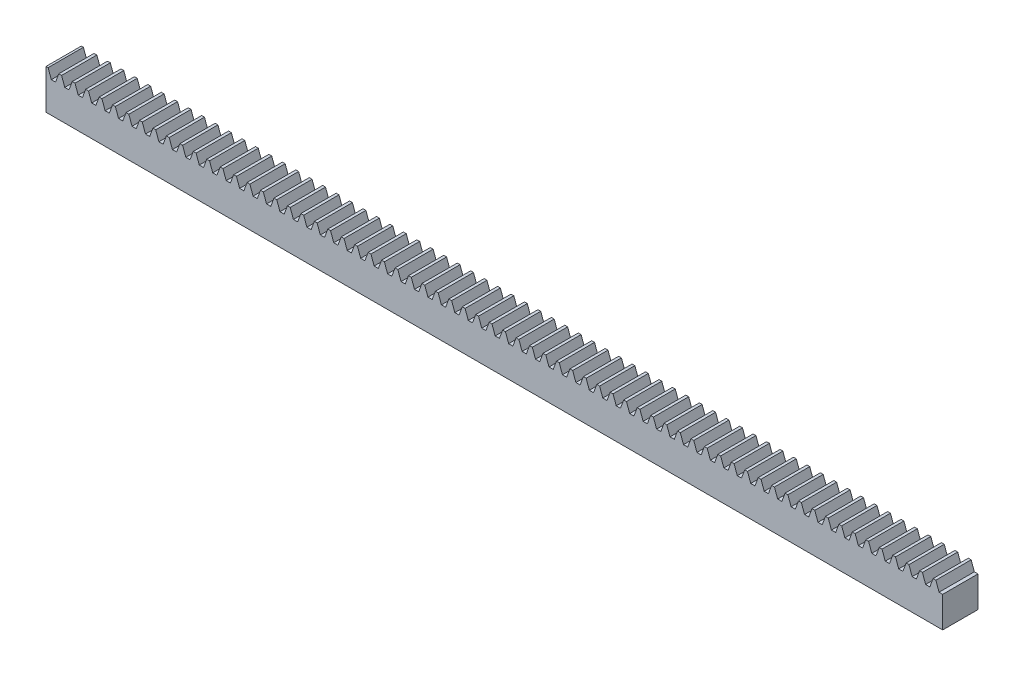
SolidWorks part; units mm, degrees
material "Nylon 101"
ref_plane "Front Plane" through (0, 0, 0) normal (0, 0, 1) x (1, 0, 0)
ref_plane "Top Plane" through (0, 0, 0) normal (0, 1, 0) x (1, 0, 0)
ref_plane "Right Plane" through (0, 0, 0) normal (1, 0, 0) x (0, 0, -1)
sketch "Sketch1" plane through (0, 0, 0) normal (0, 1, 0) x (1, 0, 0)
  line L0 (0, 0) -> (0, 4)
  line L1 (0, 4) -> (101.6, 4)
  line L2 (101.6, 4) -> (101.6, 0)
  line L3 (101.6, 0) -> (0, 0)
  dimension "D1" = 4
  dimension "D2" = 101.6
extrude "Boss-Extrude1" add sketch "Sketch1" along normal blind 4.5
sketch "Sketch2" plane through (0, 0, 0) normal (0, 0, 1) x (1, 0, 0)
  line L0 (0, 4) -> (101.6, 4) construction
  line L1 (0, 4.5) -> (0, 0) construction
  line L2 (101.6, 4.5) -> (101.6, 0) construction
  line L3 (0, 3.5) -> (101.6, 3.5) construction
  line L4 (0, 4.5) -> (101.6, 4.5) construction
  line L5 (0, 4.5) -> (0.239, 4.5) construction
  line L6 (0.239, 4.5) -> (0.603, 3.5)
  line L7 (0.603, 3.5) -> (0.842, 3.5)
  line L8 (1.081, 3.5) -> (1.445, 4.5)
  line L9 (1.445, 4.5) -> (1.684, 4.5) construction
  line L10 (0.842, 3.5) -> (1.081, 3.5)
  line L11 (0.239, 4.5) -> (1.445, 4.5)
  line L12 (1.763, 4.5) -> (2.127, 3.5)
  line L13 (2.127, 3.5) -> (2.366, 3.5)
  line L14 (2.605, 3.5) -> (2.969, 4.5)
  line L15 (2.366, 3.5) -> (2.605, 3.5)
  line L16 (1.763, 4.5) -> (2.969, 4.5)
  line L17 (1.524, 4.5) -> (1.763, 4.5) construction
  line L18 (2.969, 4.5) -> (3.208, 4.5) construction
  line L19 (3.287, 4.5) -> (3.651, 3.5)
  line L20 (3.651, 3.5) -> (3.89, 3.5)
  line L21 (4.129, 3.5) -> (4.493, 4.5)
  line L22 (3.89, 3.5) -> (4.129, 3.5)
  line L23 (3.287, 4.5) -> (4.493, 4.5)
  line L24 (3.048, 4.5) -> (3.287, 4.5) construction
  line L25 (4.493, 4.5) -> (4.732, 4.5) construction
  line L26 (4.811, 4.5) -> (5.175, 3.5)
  line L27 (5.175, 3.5) -> (5.414, 3.5)
  line L28 (5.653, 3.5) -> (6.017, 4.5)
  line L29 (5.414, 3.5) -> (5.653, 3.5)
  line L30 (4.811, 4.5) -> (6.017, 4.5)
  line L31 (4.572, 4.5) -> (4.811, 4.5) construction
  line L32 (6.017, 4.5) -> (6.256, 4.5) construction
  line L33 (6.335, 4.5) -> (6.699, 3.5)
  line L34 (6.699, 3.5) -> (6.938, 3.5)
  line L35 (7.177, 3.5) -> (7.541, 4.5)
  line L36 (6.938, 3.5) -> (7.177, 3.5)
  line L37 (6.335, 4.5) -> (7.541, 4.5)
  line L38 (6.096, 4.5) -> (6.335, 4.5) construction
  line L39 (7.541, 4.5) -> (7.78, 4.5) construction
  line L40 (7.859, 4.5) -> (8.223, 3.5)
  line L41 (8.223, 3.5) -> (8.462, 3.5)
  line L42 (8.701, 3.5) -> (9.065, 4.5)
  line L43 (8.462, 3.5) -> (8.701, 3.5)
  line L44 (7.859, 4.5) -> (9.065, 4.5)
  line L45 (7.62, 4.5) -> (7.859, 4.5) construction
  line L46 (9.065, 4.5) -> (9.304, 4.5) construction
  line L47 (9.383, 4.5) -> (9.747, 3.5)
  line L48 (9.747, 3.5) -> (9.986, 3.5)
  line L49 (10.225, 3.5) -> (10.589, 4.5)
  line L50 (9.986, 3.5) -> (10.225, 3.5)
  line L51 (9.383, 4.5) -> (10.589, 4.5)
  line L52 (9.144, 4.5) -> (9.383, 4.5) construction
  line L53 (10.589, 4.5) -> (10.828, 4.5) construction
  line L54 (10.907, 4.5) -> (11.271, 3.5)
  line L55 (11.271, 3.5) -> (11.51, 3.5)
  line L56 (11.749, 3.5) -> (12.113, 4.5)
  line L57 (11.51, 3.5) -> (11.749, 3.5)
  line L58 (10.907, 4.5) -> (12.113, 4.5)
  line L59 (10.668, 4.5) -> (10.907, 4.5) construction
  line L60 (12.113, 4.5) -> (12.352, 4.5) construction
  line L61 (12.431, 4.5) -> (12.795, 3.5)
  line L62 (12.795, 3.5) -> (13.034, 3.5)
  line L63 (13.273, 3.5) -> (13.637, 4.5)
  line L64 (13.034, 3.5) -> (13.273, 3.5)
  line L65 (12.431, 4.5) -> (13.637, 4.5)
  line L66 (12.192, 4.5) -> (12.431, 4.5) construction
  line L67 (13.637, 4.5) -> (13.876, 4.5) construction
  line L68 (13.955, 4.5) -> (14.319, 3.5)
  line L69 (14.319, 3.5) -> (14.558, 3.5)
  line L70 (14.797, 3.5) -> (15.161, 4.5)
  line L71 (14.558, 3.5) -> (14.797, 3.5)
  line L72 (13.955, 4.5) -> (15.161, 4.5)
  line L73 (13.716, 4.5) -> (13.955, 4.5) construction
  line L74 (15.161, 4.5) -> (15.4, 4.5) construction
  line L75 (15.479, 4.5) -> (15.843, 3.5)
  line L76 (15.843, 3.5) -> (16.082, 3.5)
  line L77 (16.321, 3.5) -> (16.685, 4.5)
  line L78 (16.082, 3.5) -> (16.321, 3.5)
  line L79 (15.479, 4.5) -> (16.685, 4.5)
  line L80 (15.24, 4.5) -> (15.479, 4.5) construction
  line L81 (16.685, 4.5) -> (16.924, 4.5) construction
  line L82 (17.003, 4.5) -> (17.367, 3.5)
  line L83 (17.367, 3.5) -> (17.606, 3.5)
  line L84 (17.845, 3.5) -> (18.209, 4.5)
  line L85 (17.606, 3.5) -> (17.845, 3.5)
  line L86 (17.003, 4.5) -> (18.209, 4.5)
  line L87 (16.764, 4.5) -> (17.003, 4.5) construction
  line L88 (18.209, 4.5) -> (18.448, 4.5) construction
  line L89 (18.527, 4.5) -> (18.891, 3.5)
  line L90 (18.891, 3.5) -> (19.13, 3.5)
  line L91 (19.369, 3.5) -> (19.733, 4.5)
  line L92 (19.13, 3.5) -> (19.369, 3.5)
  line L93 (18.527, 4.5) -> (19.733, 4.5)
  line L94 (18.288, 4.5) -> (18.527, 4.5) construction
  line L95 (19.733, 4.5) -> (19.972, 4.5) construction
  line L96 (20.051, 4.5) -> (20.415, 3.5)
  line L97 (20.415, 3.5) -> (20.654, 3.5)
  line L98 (20.893, 3.5) -> (21.257, 4.5)
  line L99 (20.654, 3.5) -> (20.893, 3.5)
  line L100 (20.051, 4.5) -> (21.257, 4.5)
  line L101 (19.812, 4.5) -> (20.051, 4.5) construction
  line L102 (21.257, 4.5) -> (21.496, 4.5) construction
  line L103 (21.575, 4.5) -> (21.939, 3.5)
  line L104 (21.939, 3.5) -> (22.178, 3.5)
  line L105 (22.417, 3.5) -> (22.781, 4.5)
  line L106 (22.178, 3.5) -> (22.417, 3.5)
  line L107 (21.575, 4.5) -> (22.781, 4.5)
  line L108 (21.336, 4.5) -> (21.575, 4.5) construction
  line L109 (22.781, 4.5) -> (23.02, 4.5) construction
  line L110 (23.099, 4.5) -> (23.463, 3.5)
  line L111 (23.463, 3.5) -> (23.702, 3.5)
  line L112 (23.941, 3.5) -> (24.305, 4.5)
  line L113 (23.702, 3.5) -> (23.941, 3.5)
  line L114 (23.099, 4.5) -> (24.305, 4.5)
  line L115 (22.86, 4.5) -> (23.099, 4.5) construction
  line L116 (24.305, 4.5) -> (24.544, 4.5) construction
  line L117 (24.623, 4.5) -> (24.987, 3.5)
  line L118 (24.987, 3.5) -> (25.226, 3.5)
  line L119 (25.465, 3.5) -> (25.829, 4.5)
  line L120 (25.226, 3.5) -> (25.465, 3.5)
  line L121 (24.623, 4.5) -> (25.829, 4.5)
  line L122 (24.384, 4.5) -> (24.623, 4.5) construction
  line L123 (25.829, 4.5) -> (26.068, 4.5) construction
  line L124 (26.147, 4.5) -> (26.511, 3.5)
  line L125 (26.511, 3.5) -> (26.75, 3.5)
  line L126 (26.989, 3.5) -> (27.353, 4.5)
  line L127 (26.75, 3.5) -> (26.989, 3.5)
  line L128 (26.147, 4.5) -> (27.353, 4.5)
  line L129 (25.908, 4.5) -> (26.147, 4.5) construction
  line L130 (27.353, 4.5) -> (27.592, 4.5) construction
  line L131 (27.671, 4.5) -> (28.035, 3.5)
  line L132 (28.035, 3.5) -> (28.274, 3.5)
  line L133 (28.513, 3.5) -> (28.877, 4.5)
  line L134 (28.274, 3.5) -> (28.513, 3.5)
  line L135 (27.671, 4.5) -> (28.877, 4.5)
  line L136 (27.432, 4.5) -> (27.671, 4.5) construction
  line L137 (28.877, 4.5) -> (29.116, 4.5) construction
  line L138 (29.195, 4.5) -> (29.559, 3.5)
  line L139 (29.559, 3.5) -> (29.798, 3.5)
  line L140 (30.037, 3.5) -> (30.401, 4.5)
  line L141 (29.798, 3.5) -> (30.037, 3.5)
  line L142 (29.195, 4.5) -> (30.401, 4.5)
  line L143 (28.956, 4.5) -> (29.195, 4.5) construction
  line L144 (30.401, 4.5) -> (30.64, 4.5) construction
  line L145 (30.719, 4.5) -> (31.083, 3.5)
  line L146 (31.083, 3.5) -> (31.322, 3.5)
  line L147 (31.561, 3.5) -> (31.925, 4.5)
  line L148 (31.322, 3.5) -> (31.561, 3.5)
  line L149 (30.719, 4.5) -> (31.925, 4.5)
  line L150 (30.48, 4.5) -> (30.719, 4.5) construction
  line L151 (31.925, 4.5) -> (32.164, 4.5) construction
  line L152 (32.243, 4.5) -> (32.607, 3.5)
  line L153 (32.607, 3.5) -> (32.846, 3.5)
  line L154 (33.085, 3.5) -> (33.449, 4.5)
  line L155 (32.846, 3.5) -> (33.085, 3.5)
  line L156 (32.243, 4.5) -> (33.449, 4.5)
  line L157 (32.004, 4.5) -> (32.243, 4.5) construction
  line L158 (33.449, 4.5) -> (33.688, 4.5) construction
  line L159 (33.767, 4.5) -> (34.131, 3.5)
  line L160 (34.131, 3.5) -> (34.37, 3.5)
  line L161 (34.609, 3.5) -> (34.973, 4.5)
  line L162 (34.37, 3.5) -> (34.609, 3.5)
  line L163 (33.767, 4.5) -> (34.973, 4.5)
  line L164 (33.528, 4.5) -> (33.767, 4.5) construction
  line L165 (34.973, 4.5) -> (35.212, 4.5) construction
  line L166 (35.291, 4.5) -> (35.655, 3.5)
  line L167 (35.655, 3.5) -> (35.894, 3.5)
  line L168 (36.133, 3.5) -> (36.497, 4.5)
  line L169 (35.894, 3.5) -> (36.133, 3.5)
  line L170 (35.291, 4.5) -> (36.497, 4.5)
  line L171 (35.052, 4.5) -> (35.291, 4.5) construction
  line L172 (36.497, 4.5) -> (36.736, 4.5) construction
  line L173 (36.815, 4.5) -> (37.179, 3.5)
  line L174 (37.179, 3.5) -> (37.418, 3.5)
  line L175 (37.657, 3.5) -> (38.021, 4.5)
  line L176 (37.418, 3.5) -> (37.657, 3.5)
  line L177 (36.815, 4.5) -> (38.021, 4.5)
  line L178 (36.576, 4.5) -> (36.815, 4.5) construction
  line L179 (38.021, 4.5) -> (38.26, 4.5) construction
  line L180 (38.339, 4.5) -> (38.703, 3.5)
  line L181 (38.703, 3.5) -> (38.942, 3.5)
  line L182 (39.181, 3.5) -> (39.545, 4.5)
  line L183 (38.942, 3.5) -> (39.181, 3.5)
  line L184 (38.339, 4.5) -> (39.545, 4.5)
  line L185 (38.1, 4.5) -> (38.339, 4.5) construction
  line L186 (39.545, 4.5) -> (39.784, 4.5) construction
  line L187 (39.863, 4.5) -> (40.227, 3.5)
  line L188 (40.227, 3.5) -> (40.466, 3.5)
  line L189 (40.705, 3.5) -> (41.069, 4.5)
  line L190 (40.466, 3.5) -> (40.705, 3.5)
  line L191 (39.863, 4.5) -> (41.069, 4.5)
  line L192 (39.624, 4.5) -> (39.863, 4.5) construction
  line L193 (41.069, 4.5) -> (41.308, 4.5) construction
  line L194 (41.387, 4.5) -> (41.751, 3.5)
  line L195 (41.751, 3.5) -> (41.99, 3.5)
  line L196 (42.229, 3.5) -> (42.593, 4.5)
  line L197 (41.99, 3.5) -> (42.229, 3.5)
  line L198 (41.387, 4.5) -> (42.593, 4.5)
  line L199 (41.148, 4.5) -> (41.387, 4.5) construction
  line L200 (42.593, 4.5) -> (42.832, 4.5) construction
  line L201 (42.911, 4.5) -> (43.275, 3.5)
  line L202 (43.275, 3.5) -> (43.514, 3.5)
  line L203 (43.753, 3.5) -> (44.117, 4.5)
  line L204 (43.514, 3.5) -> (43.753, 3.5)
  line L205 (42.911, 4.5) -> (44.117, 4.5)
  line L206 (42.672, 4.5) -> (42.911, 4.5) construction
  line L207 (44.117, 4.5) -> (44.356, 4.5) construction
  line L208 (44.435, 4.5) -> (44.799, 3.5)
  line L209 (44.799, 3.5) -> (45.038, 3.5)
  line L210 (45.277, 3.5) -> (45.641, 4.5)
  line L211 (45.038, 3.5) -> (45.277, 3.5)
  line L212 (44.435, 4.5) -> (45.641, 4.5)
  line L213 (44.196, 4.5) -> (44.435, 4.5) construction
  line L214 (45.641, 4.5) -> (45.88, 4.5) construction
  line L215 (45.959, 4.5) -> (46.323, 3.5)
  line L216 (46.323, 3.5) -> (46.562, 3.5)
  line L217 (46.801, 3.5) -> (47.165, 4.5)
  line L218 (46.562, 3.5) -> (46.801, 3.5)
  line L219 (45.959, 4.5) -> (47.165, 4.5)
  line L220 (45.72, 4.5) -> (45.959, 4.5) construction
  line L221 (47.165, 4.5) -> (47.404, 4.5) construction
  line L222 (47.483, 4.5) -> (47.847, 3.5)
  line L223 (47.847, 3.5) -> (48.086, 3.5)
  line L224 (48.325, 3.5) -> (48.689, 4.5)
  line L225 (48.086, 3.5) -> (48.325, 3.5)
  line L226 (47.483, 4.5) -> (48.689, 4.5)
  line L227 (47.244, 4.5) -> (47.483, 4.5) construction
  line L228 (48.689, 4.5) -> (48.928, 4.5) construction
  line L229 (49.007, 4.5) -> (49.371, 3.5)
  line L230 (49.371, 3.5) -> (49.61, 3.5)
  line L231 (49.849, 3.5) -> (50.213, 4.5)
  line L232 (49.61, 3.5) -> (49.849, 3.5)
  line L233 (49.007, 4.5) -> (50.213, 4.5)
  line L234 (48.768, 4.5) -> (49.007, 4.5) construction
  line L235 (50.213, 4.5) -> (50.452, 4.5) construction
  line L236 (50.531, 4.5) -> (50.895, 3.5)
  line L237 (50.895, 3.5) -> (51.134, 3.5)
  line L238 (51.373, 3.5) -> (51.737, 4.5)
  line L239 (51.134, 3.5) -> (51.373, 3.5)
  line L240 (50.531, 4.5) -> (51.737, 4.5)
  line L241 (50.292, 4.5) -> (50.531, 4.5) construction
  line L242 (51.737, 4.5) -> (51.976, 4.5) construction
  line L243 (52.055, 4.5) -> (52.419, 3.5)
  line L244 (52.419, 3.5) -> (52.658, 3.5)
  line L245 (52.897, 3.5) -> (53.261, 4.5)
  line L246 (52.658, 3.5) -> (52.897, 3.5)
  line L247 (52.055, 4.5) -> (53.261, 4.5)
  line L248 (51.816, 4.5) -> (52.055, 4.5) construction
  line L249 (53.261, 4.5) -> (53.5, 4.5) construction
  line L250 (53.579, 4.5) -> (53.943, 3.5)
  line L251 (53.943, 3.5) -> (54.182, 3.5)
  line L252 (54.421, 3.5) -> (54.785, 4.5)
  line L253 (54.182, 3.5) -> (54.421, 3.5)
  line L254 (53.579, 4.5) -> (54.785, 4.5)
  line L255 (53.34, 4.5) -> (53.579, 4.5) construction
  line L256 (54.785, 4.5) -> (55.024, 4.5) construction
  line L257 (55.103, 4.5) -> (55.467, 3.5)
  line L258 (55.467, 3.5) -> (55.706, 3.5)
  line L259 (55.945, 3.5) -> (56.309, 4.5)
  line L260 (55.706, 3.5) -> (55.945, 3.5)
  line L261 (55.103, 4.5) -> (56.309, 4.5)
  line L262 (54.864, 4.5) -> (55.103, 4.5) construction
  line L263 (56.309, 4.5) -> (56.548, 4.5) construction
  line L264 (56.627, 4.5) -> (56.991, 3.5)
  line L265 (56.991, 3.5) -> (57.23, 3.5)
  line L266 (57.469, 3.5) -> (57.833, 4.5)
  line L267 (57.23, 3.5) -> (57.469, 3.5)
  line L268 (56.627, 4.5) -> (57.833, 4.5)
  line L269 (56.388, 4.5) -> (56.627, 4.5) construction
  line L270 (57.833, 4.5) -> (58.072, 4.5) construction
  line L271 (58.151, 4.5) -> (58.515, 3.5)
  line L272 (58.515, 3.5) -> (58.754, 3.5)
  line L273 (58.993, 3.5) -> (59.357, 4.5)
  line L274 (58.754, 3.5) -> (58.993, 3.5)
  line L275 (58.151, 4.5) -> (59.357, 4.5)
  line L276 (57.912, 4.5) -> (58.151, 4.5) construction
  line L277 (59.357, 4.5) -> (59.596, 4.5) construction
  line L278 (59.675, 4.5) -> (60.039, 3.5)
  line L279 (60.039, 3.5) -> (60.278, 3.5)
  line L280 (60.517, 3.5) -> (60.881, 4.5)
  line L281 (60.278, 3.5) -> (60.517, 3.5)
  line L282 (59.675, 4.5) -> (60.881, 4.5)
  line L283 (59.436, 4.5) -> (59.675, 4.5) construction
  line L284 (60.881, 4.5) -> (61.12, 4.5) construction
  line L285 (61.199, 4.5) -> (61.563, 3.5)
  line L286 (61.563, 3.5) -> (61.802, 3.5)
  line L287 (62.041, 3.5) -> (62.405, 4.5)
  line L288 (61.802, 3.5) -> (62.041, 3.5)
  line L289 (61.199, 4.5) -> (62.405, 4.5)
  line L290 (60.96, 4.5) -> (61.199, 4.5) construction
  line L291 (62.405, 4.5) -> (62.644, 4.5) construction
  line L292 (62.723, 4.5) -> (63.087, 3.5)
  line L293 (63.087, 3.5) -> (63.326, 3.5)
  line L294 (63.565, 3.5) -> (63.929, 4.5)
  line L295 (63.326, 3.5) -> (63.565, 3.5)
  line L296 (62.723, 4.5) -> (63.929, 4.5)
  line L297 (62.484, 4.5) -> (62.723, 4.5) construction
  line L298 (63.929, 4.5) -> (64.168, 4.5) construction
  line L299 (64.247, 4.5) -> (64.611, 3.5)
  line L300 (64.611, 3.5) -> (64.85, 3.5)
  line L301 (65.089, 3.5) -> (65.453, 4.5)
  line L302 (64.85, 3.5) -> (65.089, 3.5)
  line L303 (64.247, 4.5) -> (65.453, 4.5)
  line L304 (64.008, 4.5) -> (64.247, 4.5) construction
  line L305 (65.453, 4.5) -> (65.692, 4.5) construction
  line L306 (65.771, 4.5) -> (66.135, 3.5)
  line L307 (66.135, 3.5) -> (66.374, 3.5)
  line L308 (66.613, 3.5) -> (66.977, 4.5)
  line L309 (66.374, 3.5) -> (66.613, 3.5)
  line L310 (65.771, 4.5) -> (66.977, 4.5)
  line L311 (65.532, 4.5) -> (65.771, 4.5) construction
  line L312 (66.977, 4.5) -> (67.216, 4.5) construction
  line L313 (67.295, 4.5) -> (67.659, 3.5)
  line L314 (67.659, 3.5) -> (67.898, 3.5)
  line L315 (68.137, 3.5) -> (68.501, 4.5)
  line L316 (67.898, 3.5) -> (68.137, 3.5)
  line L317 (67.295, 4.5) -> (68.501, 4.5)
  line L318 (67.056, 4.5) -> (67.295, 4.5) construction
  line L319 (68.501, 4.5) -> (68.74, 4.5) construction
  line L320 (68.819, 4.5) -> (69.183, 3.5)
  line L321 (69.183, 3.5) -> (69.422, 3.5)
  line L322 (69.661, 3.5) -> (70.025, 4.5)
  line L323 (69.422, 3.5) -> (69.661, 3.5)
  line L324 (68.819, 4.5) -> (70.025, 4.5)
  line L325 (68.58, 4.5) -> (68.819, 4.5) construction
  line L326 (70.025, 4.5) -> (70.264, 4.5) construction
  line L327 (70.343, 4.5) -> (70.707, 3.5)
  line L328 (70.707, 3.5) -> (70.946, 3.5)
  line L329 (71.185, 3.5) -> (71.549, 4.5)
  line L330 (70.946, 3.5) -> (71.185, 3.5)
  line L331 (70.343, 4.5) -> (71.549, 4.5)
  line L332 (70.104, 4.5) -> (70.343, 4.5) construction
  line L333 (71.549, 4.5) -> (71.788, 4.5) construction
  line L334 (71.867, 4.5) -> (72.231, 3.5)
  line L335 (72.231, 3.5) -> (72.47, 3.5)
  line L336 (72.709, 3.5) -> (73.073, 4.5)
  line L337 (72.47, 3.5) -> (72.709, 3.5)
  line L338 (71.867, 4.5) -> (73.073, 4.5)
  line L339 (71.628, 4.5) -> (71.867, 4.5) construction
  line L340 (73.073, 4.5) -> (73.312, 4.5) construction
  line L341 (73.391, 4.5) -> (73.755, 3.5)
  line L342 (73.755, 3.5) -> (73.994, 3.5)
  line L343 (74.233, 3.5) -> (74.597, 4.5)
  line L344 (73.994, 3.5) -> (74.233, 3.5)
  line L345 (73.391, 4.5) -> (74.597, 4.5)
  line L346 (73.152, 4.5) -> (73.391, 4.5) construction
  line L347 (74.597, 4.5) -> (74.836, 4.5) construction
  line L348 (74.915, 4.5) -> (75.279, 3.5)
  line L349 (75.279, 3.5) -> (75.518, 3.5)
  line L350 (75.757, 3.5) -> (76.121, 4.5)
  line L351 (75.518, 3.5) -> (75.757, 3.5)
  line L352 (74.915, 4.5) -> (76.121, 4.5)
  line L353 (74.676, 4.5) -> (74.915, 4.5) construction
  line L354 (76.121, 4.5) -> (76.36, 4.5) construction
  line L355 (76.439, 4.5) -> (76.803, 3.5)
  line L356 (76.803, 3.5) -> (77.042, 3.5)
  line L357 (77.281, 3.5) -> (77.645, 4.5)
  line L358 (77.042, 3.5) -> (77.281, 3.5)
  line L359 (76.439, 4.5) -> (77.645, 4.5)
  line L360 (76.2, 4.5) -> (76.439, 4.5) construction
  line L361 (77.645, 4.5) -> (77.884, 4.5) construction
  line L362 (77.963, 4.5) -> (78.327, 3.5)
  line L363 (78.327, 3.5) -> (78.566, 3.5)
  line L364 (78.805, 3.5) -> (79.169, 4.5)
  line L365 (78.566, 3.5) -> (78.805, 3.5)
  line L366 (77.963, 4.5) -> (79.169, 4.5)
  line L367 (77.724, 4.5) -> (77.963, 4.5) construction
  line L368 (79.169, 4.5) -> (79.408, 4.5) construction
  line L369 (79.487, 4.5) -> (79.851, 3.5)
  line L370 (79.851, 3.5) -> (80.09, 3.5)
  line L371 (80.329, 3.5) -> (80.693, 4.5)
  line L372 (80.09, 3.5) -> (80.329, 3.5)
  line L373 (79.487, 4.5) -> (80.693, 4.5)
  line L374 (79.248, 4.5) -> (79.487, 4.5) construction
  line L375 (80.693, 4.5) -> (80.932, 4.5) construction
  line L376 (81.011, 4.5) -> (81.375, 3.5)
  line L377 (81.375, 3.5) -> (81.614, 3.5)
  line L378 (81.853, 3.5) -> (82.217, 4.5)
  line L379 (81.614, 3.5) -> (81.853, 3.5)
  line L380 (81.011, 4.5) -> (82.217, 4.5)
  line L381 (80.772, 4.5) -> (81.011, 4.5) construction
  line L382 (82.217, 4.5) -> (82.456, 4.5) construction
  line L383 (82.535, 4.5) -> (82.899, 3.5)
  line L384 (82.899, 3.5) -> (83.138, 3.5)
  line L385 (83.377, 3.5) -> (83.741, 4.5)
  line L386 (83.138, 3.5) -> (83.377, 3.5)
  line L387 (82.535, 4.5) -> (83.741, 4.5)
  line L388 (82.296, 4.5) -> (82.535, 4.5) construction
  line L389 (83.741, 4.5) -> (83.98, 4.5) construction
  line L390 (84.059, 4.5) -> (84.423, 3.5)
  line L391 (84.423, 3.5) -> (84.662, 3.5)
  line L392 (84.901, 3.5) -> (85.265, 4.5)
  line L393 (84.662, 3.5) -> (84.901, 3.5)
  line L394 (84.059, 4.5) -> (85.265, 4.5)
  line L395 (83.82, 4.5) -> (84.059, 4.5) construction
  line L396 (85.265, 4.5) -> (85.504, 4.5) construction
  line L397 (85.583, 4.5) -> (85.947, 3.5)
  line L398 (85.947, 3.5) -> (86.186, 3.5)
  line L399 (86.425, 3.5) -> (86.789, 4.5)
  line L400 (86.186, 3.5) -> (86.425, 3.5)
  line L401 (85.583, 4.5) -> (86.789, 4.5)
  line L402 (85.344, 4.5) -> (85.583, 4.5) construction
  line L403 (86.789, 4.5) -> (87.028, 4.5) construction
  line L404 (87.107, 4.5) -> (87.471, 3.5)
  line L405 (87.471, 3.5) -> (87.71, 3.5)
  line L406 (87.949, 3.5) -> (88.313, 4.5)
  line L407 (87.71, 3.5) -> (87.949, 3.5)
  line L408 (87.107, 4.5) -> (88.313, 4.5)
  line L409 (86.868, 4.5) -> (87.107, 4.5) construction
  line L410 (88.313, 4.5) -> (88.552, 4.5) construction
  line L411 (88.631, 4.5) -> (88.995, 3.5)
  line L412 (88.995, 3.5) -> (89.234, 3.5)
  line L413 (89.473, 3.5) -> (89.837, 4.5)
  line L414 (89.234, 3.5) -> (89.473, 3.5)
  line L415 (88.631, 4.5) -> (89.837, 4.5)
  line L416 (88.392, 4.5) -> (88.631, 4.5) construction
  line L417 (89.837, 4.5) -> (90.076, 4.5) construction
  line L418 (90.155, 4.5) -> (90.519, 3.5)
  line L419 (90.519, 3.5) -> (90.758, 3.5)
  line L420 (90.997, 3.5) -> (91.361, 4.5)
  line L421 (90.758, 3.5) -> (90.997, 3.5)
  line L422 (90.155, 4.5) -> (91.361, 4.5)
  line L423 (89.916, 4.5) -> (90.155, 4.5) construction
  line L424 (91.361, 4.5) -> (91.6, 4.5) construction
  line L425 (91.679, 4.5) -> (92.043, 3.5)
  line L426 (92.043, 3.5) -> (92.282, 3.5)
  line L427 (92.521, 3.5) -> (92.885, 4.5)
  line L428 (92.282, 3.5) -> (92.521, 3.5)
  line L429 (91.679, 4.5) -> (92.885, 4.5)
  line L430 (91.44, 4.5) -> (91.679, 4.5) construction
  line L431 (92.885, 4.5) -> (93.124, 4.5) construction
  line L432 (93.203, 4.5) -> (93.567, 3.5)
  line L433 (93.567, 3.5) -> (93.806, 3.5)
  line L434 (94.045, 3.5) -> (94.409, 4.5)
  line L435 (93.806, 3.5) -> (94.045, 3.5)
  line L436 (93.203, 4.5) -> (94.409, 4.5)
  line L437 (92.964, 4.5) -> (93.203, 4.5) construction
  line L438 (94.409, 4.5) -> (94.648, 4.5) construction
  line L439 (94.727, 4.5) -> (95.091, 3.5)
  line L440 (95.091, 3.5) -> (95.33, 3.5)
  line L441 (95.569, 3.5) -> (95.933, 4.5)
  line L442 (95.33, 3.5) -> (95.569, 3.5)
  line L443 (94.727, 4.5) -> (95.933, 4.5)
  line L444 (94.488, 4.5) -> (94.727, 4.5) construction
  line L445 (95.933, 4.5) -> (96.172, 4.5) construction
  line L446 (96.251, 4.5) -> (96.615, 3.5)
  line L447 (96.615, 3.5) -> (96.854, 3.5)
  line L448 (97.093, 3.5) -> (97.457, 4.5)
  line L449 (96.854, 3.5) -> (97.093, 3.5)
  line L450 (96.251, 4.5) -> (97.457, 4.5)
  line L451 (96.012, 4.5) -> (96.251, 4.5) construction
  line L452 (97.457, 4.5) -> (97.696, 4.5) construction
  line L453 (97.775, 4.5) -> (98.139, 3.5)
  line L454 (98.139, 3.5) -> (98.378, 3.5)
  line L455 (98.617, 3.5) -> (98.981, 4.5)
  line L456 (98.378, 3.5) -> (98.617, 3.5)
  line L457 (97.775, 4.5) -> (98.981, 4.5)
  line L458 (97.536, 4.5) -> (97.775, 4.5) construction
  line L459 (98.981, 4.5) -> (99.22, 4.5) construction
  line L460 (99.299, 4.5) -> (99.663, 3.5)
  line L461 (99.663, 3.5) -> (99.902, 3.5)
  line L462 (100.141, 3.5) -> (100.505, 4.5)
  line L463 (99.902, 3.5) -> (100.141, 3.5)
  line L464 (99.299, 4.5) -> (100.505, 4.5)
  line L465 (99.06, 4.5) -> (99.299, 4.5) construction
  line L466 (100.505, 4.5) -> (100.744, 4.5) construction
  line L467 (100.823, 4.5) -> (101.187, 3.5)
  line L468 (101.187, 3.5) -> (101.426, 3.5)
  line L469 (101.665, 3.5) -> (102.029, 4.5)
  line L470 (101.426, 3.5) -> (101.665, 3.5)
  line L471 (100.823, 4.5) -> (102.029, 4.5)
  line L472 (100.584, 4.5) -> (100.823, 4.5) construction
  line L473 (102.029, 4.5) -> (102.268, 4.5) construction
  line L474 (102.347, 4.5) -> (102.711, 3.5)
  line L475 (102.711, 3.5) -> (102.95, 3.5)
  line L476 (103.189, 3.5) -> (103.553, 4.5)
  line L477 (102.95, 3.5) -> (103.189, 3.5)
  line L478 (102.347, 4.5) -> (103.553, 4.5)
  line L479 (102.108, 4.5) -> (102.347, 4.5) construction
  line L480 (103.553, 4.5) -> (103.792, 4.5) construction
  line L481 (103.871, 4.5) -> (104.235, 3.5)
  line L482 (104.235, 3.5) -> (104.474, 3.5)
  line L483 (104.713, 3.5) -> (105.077, 4.5)
  line L484 (104.474, 3.5) -> (104.713, 3.5)
  line L485 (103.871, 4.5) -> (105.077, 4.5)
  line L486 (103.632, 4.5) -> (103.871, 4.5) construction
  line L487 (105.077, 4.5) -> (105.316, 4.5) construction
  line L488 (105.395, 4.5) -> (105.759, 3.5)
  line L489 (105.759, 3.5) -> (105.998, 3.5)
  line L490 (106.237, 3.5) -> (106.601, 4.5)
  line L491 (105.998, 3.5) -> (106.237, 3.5)
  line L492 (105.395, 4.5) -> (106.601, 4.5)
  line L493 (105.156, 4.5) -> (105.395, 4.5) construction
  line L494 (106.601, 4.5) -> (106.84, 4.5) construction
  line L495 (106.919, 4.5) -> (107.283, 3.5)
  line L496 (107.283, 3.5) -> (107.522, 3.5)
  line L497 (107.761, 3.5) -> (108.125, 4.5)
  line L498 (107.522, 3.5) -> (107.761, 3.5)
  line L499 (106.919, 4.5) -> (108.125, 4.5)
  line L500 (106.68, 4.5) -> (106.919, 4.5) construction
  line L501 (108.125, 4.5) -> (108.364, 4.5) construction
  line L502 (108.443, 4.5) -> (108.807, 3.5)
  line L503 (108.807, 3.5) -> (109.046, 3.5)
  line L504 (109.285, 3.5) -> (109.649, 4.5)
  line L505 (109.046, 3.5) -> (109.285, 3.5)
  line L506 (108.443, 4.5) -> (109.649, 4.5)
  line L507 (108.204, 4.5) -> (108.443, 4.5) construction
  line L508 (109.649, 4.5) -> (109.888, 4.5) construction
  line L509 (109.967, 4.5) -> (110.331, 3.5)
  line L510 (110.331, 3.5) -> (110.57, 3.5)
  line L511 (110.809, 3.5) -> (111.173, 4.5)
  line L512 (110.57, 3.5) -> (110.809, 3.5)
  line L513 (109.967, 4.5) -> (111.173, 4.5)
  line L514 (109.728, 4.5) -> (109.967, 4.5) construction
  line L515 (111.173, 4.5) -> (111.412, 4.5) construction
  line L516 (111.491, 4.5) -> (111.855, 3.5)
  line L517 (111.855, 3.5) -> (112.094, 3.5)
  line L518 (112.333, 3.5) -> (112.697, 4.5)
  line L519 (112.094, 3.5) -> (112.333, 3.5)
  line L520 (111.491, 4.5) -> (112.697, 4.5)
  line L521 (111.252, 4.5) -> (111.491, 4.5) construction
  line L522 (112.697, 4.5) -> (112.936, 4.5) construction
  line L523 (113.015, 4.5) -> (113.379, 3.5)
  line L524 (113.379, 3.5) -> (113.618, 3.5)
  line L525 (113.857, 3.5) -> (114.221, 4.5)
  line L526 (113.618, 3.5) -> (113.857, 3.5)
  line L527 (113.015, 4.5) -> (114.221, 4.5)
  line L528 (112.776, 4.5) -> (113.015, 4.5) construction
  line L529 (114.221, 4.5) -> (114.46, 4.5) construction
  line L530 (114.539, 4.5) -> (114.903, 3.5)
  line L531 (114.903, 3.5) -> (115.142, 3.5)
  line L532 (115.381, 3.5) -> (115.745, 4.5)
  line L533 (115.142, 3.5) -> (115.381, 3.5)
  line L534 (114.539, 4.5) -> (115.745, 4.5)
  line L535 (114.3, 4.5) -> (114.539, 4.5) construction
  line L536 (115.745, 4.5) -> (115.984, 4.5) construction
  line L537 (116.063, 4.5) -> (116.427, 3.5)
  line L538 (116.427, 3.5) -> (116.666, 3.5)
  line L539 (116.905, 3.5) -> (117.269, 4.5)
  line L540 (116.666, 3.5) -> (116.905, 3.5)
  line L541 (116.063, 4.5) -> (117.269, 4.5)
  line L542 (115.824, 4.5) -> (116.063, 4.5) construction
  line L543 (117.269, 4.5) -> (117.508, 4.5) construction
  line L544 (117.587, 4.5) -> (117.951, 3.5)
  line L545 (117.951, 3.5) -> (118.19, 3.5)
  line L546 (118.429, 3.5) -> (118.793, 4.5)
  line L547 (118.19, 3.5) -> (118.429, 3.5)
  line L548 (117.587, 4.5) -> (118.793, 4.5)
  line L549 (117.348, 4.5) -> (117.587, 4.5) construction
  line L550 (118.793, 4.5) -> (119.032, 4.5) construction
  line L551 (119.111, 4.5) -> (119.475, 3.5)
  line L552 (119.475, 3.5) -> (119.714, 3.5)
  line L553 (119.953, 3.5) -> (120.317, 4.5)
  line L554 (119.714, 3.5) -> (119.953, 3.5)
  line L555 (119.111, 4.5) -> (120.317, 4.5)
  line L556 (118.872, 4.5) -> (119.111, 4.5) construction
  line L557 (120.317, 4.5) -> (120.556, 4.5) construction
  line L558 (120.635, 4.5) -> (120.999, 3.5)
  line L559 (120.999, 3.5) -> (121.238, 3.5)
  line L560 (121.477, 3.5) -> (121.841, 4.5)
  line L561 (121.238, 3.5) -> (121.477, 3.5)
  line L562 (120.635, 4.5) -> (121.841, 4.5)
  line L563 (120.396, 4.5) -> (120.635, 4.5) construction
  line L564 (121.841, 4.5) -> (122.08, 4.5) construction
  line L565 (122.159, 4.5) -> (122.523, 3.5)
  line L566 (122.523, 3.5) -> (122.762, 3.5)
  line L567 (123.001, 3.5) -> (123.365, 4.5)
  line L568 (122.762, 3.5) -> (123.001, 3.5)
  line L569 (122.159, 4.5) -> (123.365, 4.5)
  line L570 (121.92, 4.5) -> (122.159, 4.5) construction
  line L571 (123.365, 4.5) -> (123.604, 4.5) construction
  line L572 (123.683, 4.5) -> (124.047, 3.5)
  line L573 (124.047, 3.5) -> (124.286, 3.5)
  line L574 (124.525, 3.5) -> (124.889, 4.5)
  line L575 (124.286, 3.5) -> (124.525, 3.5)
  line L576 (123.683, 4.5) -> (124.889, 4.5)
  line L577 (123.444, 4.5) -> (123.683, 4.5) construction
  line L578 (124.889, 4.5) -> (125.128, 4.5) construction
  line L579 (125.207, 4.5) -> (125.571, 3.5)
  line L580 (125.571, 3.5) -> (125.81, 3.5)
  line L581 (126.049, 3.5) -> (126.413, 4.5)
  line L582 (125.81, 3.5) -> (126.049, 3.5)
  line L583 (125.207, 4.5) -> (126.413, 4.5)
  line L584 (124.968, 4.5) -> (125.207, 4.5) construction
  line L585 (126.413, 4.5) -> (126.652, 4.5) construction
  line L586 (126.731, 4.5) -> (127.095, 3.5)
  line L587 (127.095, 3.5) -> (127.334, 3.5)
  line L588 (127.573, 3.5) -> (127.937, 4.5)
  line L589 (127.334, 3.5) -> (127.573, 3.5)
  line L590 (126.731, 4.5) -> (127.937, 4.5)
  line L591 (126.492, 4.5) -> (126.731, 4.5) construction
  line L592 (127.937, 4.5) -> (128.176, 4.5) construction
  line L593 (128.255, 4.5) -> (128.619, 3.5)
  line L594 (128.619, 3.5) -> (128.858, 3.5)
  line L595 (129.097, 3.5) -> (129.461, 4.5)
  line L596 (128.858, 3.5) -> (129.097, 3.5)
  line L597 (128.255, 4.5) -> (129.461, 4.5)
  line L598 (128.016, 4.5) -> (128.255, 4.5) construction
  line L599 (129.461, 4.5) -> (129.7, 4.5) construction
  line L600 (129.779, 4.5) -> (130.143, 3.5)
  line L601 (130.143, 3.5) -> (130.382, 3.5)
  line L602 (130.621, 3.5) -> (130.985, 4.5)
  line L603 (130.382, 3.5) -> (130.621, 3.5)
  line L604 (129.779, 4.5) -> (130.985, 4.5)
  line L605 (129.54, 4.5) -> (129.779, 4.5) construction
  line L606 (130.985, 4.5) -> (131.224, 4.5) construction
  line L607 (131.303, 4.5) -> (131.667, 3.5)
  line L608 (131.667, 3.5) -> (131.906, 3.5)
  line L609 (132.145, 3.5) -> (132.509, 4.5)
  line L610 (131.906, 3.5) -> (132.145, 3.5)
  line L611 (131.303, 4.5) -> (132.509, 4.5)
  line L612 (131.064, 4.5) -> (131.303, 4.5) construction
  line L613 (132.509, 4.5) -> (132.748, 4.5) construction
  line L614 (132.827, 4.5) -> (133.191, 3.5)
  line L615 (133.191, 3.5) -> (133.43, 3.5)
  line L616 (133.669, 3.5) -> (134.033, 4.5)
  line L617 (133.43, 3.5) -> (133.669, 3.5)
  line L618 (132.827, 4.5) -> (134.033, 4.5)
  line L619 (132.588, 4.5) -> (132.827, 4.5) construction
  line L620 (134.033, 4.5) -> (134.272, 4.5) construction
  line L621 (134.351, 4.5) -> (134.715, 3.5)
  line L622 (134.715, 3.5) -> (134.954, 3.5)
  line L623 (135.193, 3.5) -> (135.557, 4.5)
  line L624 (134.954, 3.5) -> (135.193, 3.5)
  line L625 (134.351, 4.5) -> (135.557, 4.5)
  line L626 (134.112, 4.5) -> (134.351, 4.5) construction
  line L627 (135.557, 4.5) -> (135.796, 4.5) construction
  line L628 (135.875, 4.5) -> (136.239, 3.5)
  line L629 (136.239, 3.5) -> (136.478, 3.5)
  line L630 (136.717, 3.5) -> (137.081, 4.5)
  line L631 (136.478, 3.5) -> (136.717, 3.5)
  line L632 (135.875, 4.5) -> (137.081, 4.5)
  line L633 (135.636, 4.5) -> (135.875, 4.5) construction
  line L634 (137.081, 4.5) -> (137.32, 4.5) construction
  line L635 (137.399, 4.5) -> (137.763, 3.5)
  line L636 (137.763, 3.5) -> (138.002, 3.5)
  line L637 (138.241, 3.5) -> (138.605, 4.5)
  line L638 (138.002, 3.5) -> (138.241, 3.5)
  line L639 (137.399, 4.5) -> (138.605, 4.5)
  line L640 (137.16, 4.5) -> (137.399, 4.5) construction
  line L641 (138.605, 4.5) -> (138.844, 4.5) construction
  line L642 (138.923, 4.5) -> (139.287, 3.5)
  line L643 (139.287, 3.5) -> (139.526, 3.5)
  line L644 (139.765, 3.5) -> (140.129, 4.5)
  line L645 (139.526, 3.5) -> (139.765, 3.5)
  line L646 (138.923, 4.5) -> (140.129, 4.5)
  line L647 (138.684, 4.5) -> (138.923, 4.5) construction
  line L648 (140.129, 4.5) -> (140.368, 4.5) construction
  line L649 (140.447, 4.5) -> (140.811, 3.5)
  line L650 (140.811, 3.5) -> (141.05, 3.5)
  line L651 (141.289, 3.5) -> (141.653, 4.5)
  line L652 (141.05, 3.5) -> (141.289, 3.5)
  line L653 (140.447, 4.5) -> (141.653, 4.5)
  line L654 (140.208, 4.5) -> (140.447, 4.5) construction
  line L655 (141.653, 4.5) -> (141.892, 4.5) construction
  line L656 (141.971, 4.5) -> (142.335, 3.5)
  line L657 (142.335, 3.5) -> (142.574, 3.5)
  line L658 (142.813, 3.5) -> (143.177, 4.5)
  line L659 (142.574, 3.5) -> (142.813, 3.5)
  line L660 (141.971, 4.5) -> (143.177, 4.5)
  line L661 (141.732, 4.5) -> (141.971, 4.5) construction
  line L662 (143.177, 4.5) -> (143.416, 4.5) construction
  line L663 (143.495, 4.5) -> (143.859, 3.5)
  line L664 (143.859, 3.5) -> (144.098, 3.5)
  line L665 (144.337, 3.5) -> (144.701, 4.5)
  line L666 (144.098, 3.5) -> (144.337, 3.5)
  line L667 (143.495, 4.5) -> (144.701, 4.5)
  line L668 (143.256, 4.5) -> (143.495, 4.5) construction
  line L669 (144.701, 4.5) -> (144.94, 4.5) construction
  line L670 (145.019, 4.5) -> (145.383, 3.5)
  line L671 (145.383, 3.5) -> (145.622, 3.5)
  line L672 (145.861, 3.5) -> (146.225, 4.5)
  line L673 (145.622, 3.5) -> (145.861, 3.5)
  line L674 (145.019, 4.5) -> (146.225, 4.5)
  line L675 (144.78, 4.5) -> (145.019, 4.5) construction
  line L676 (146.225, 4.5) -> (146.464, 4.5) construction
  line L677 (146.543, 4.5) -> (146.907, 3.5)
  line L678 (146.907, 3.5) -> (147.146, 3.5)
  line L679 (147.385, 3.5) -> (147.749, 4.5)
  line L680 (147.146, 3.5) -> (147.385, 3.5)
  line L681 (146.543, 4.5) -> (147.749, 4.5)
  line L682 (146.304, 4.5) -> (146.543, 4.5) construction
  line L683 (147.749, 4.5) -> (147.988, 4.5) construction
  line L684 (148.067, 4.5) -> (148.431, 3.5)
  line L685 (148.431, 3.5) -> (148.67, 3.5)
  line L686 (148.909, 3.5) -> (149.273, 4.5)
  line L687 (148.67, 3.5) -> (148.909, 3.5)
  line L688 (148.067, 4.5) -> (149.273, 4.5)
  line L689 (147.828, 4.5) -> (148.067, 4.5) construction
  line L690 (149.273, 4.5) -> (149.512, 4.5) construction
  line L691 (149.591, 4.5) -> (149.955, 3.5)
  line L692 (149.955, 3.5) -> (150.194, 3.5)
  line L693 (150.433, 3.5) -> (150.797, 4.5)
  line L694 (150.194, 3.5) -> (150.433, 3.5)
  line L695 (149.591, 4.5) -> (150.797, 4.5)
  line L696 (149.352, 4.5) -> (149.591, 4.5) construction
  line L697 (150.797, 4.5) -> (151.036, 4.5) construction
  line L698 (151.115, 4.5) -> (151.479, 3.5)
  line L699 (151.479, 3.5) -> (151.718, 3.5)
  line L700 (151.957, 3.5) -> (152.321, 4.5)
  line L701 (151.718, 3.5) -> (151.957, 3.5)
  line L702 (151.115, 4.5) -> (152.321, 4.5)
  line L703 (150.876, 4.5) -> (151.115, 4.5) construction
  line L704 (152.321, 4.5) -> (152.56, 4.5) construction
  line L705 (152.639, 4.5) -> (153.003, 3.5)
  line L706 (153.003, 3.5) -> (153.242, 3.5)
  line L707 (153.481, 3.5) -> (153.845, 4.5)
  line L708 (153.242, 3.5) -> (153.481, 3.5)
  line L709 (152.639, 4.5) -> (153.845, 4.5)
  line L710 (152.4, 4.5) -> (152.639, 4.5) construction
  line L711 (153.845, 4.5) -> (154.084, 4.5) construction
  line L712 (154.163, 4.5) -> (154.527, 3.5)
  line L713 (154.527, 3.5) -> (154.766, 3.5)
  line L714 (155.005, 3.5) -> (155.369, 4.5)
  line L715 (154.766, 3.5) -> (155.005, 3.5)
  line L716 (154.163, 4.5) -> (155.369, 4.5)
  line L717 (153.924, 4.5) -> (154.163, 4.5) construction
  line L718 (155.369, 4.5) -> (155.608, 4.5) construction
  line L719 (155.687, 4.5) -> (156.051, 3.5)
  line L720 (156.051, 3.5) -> (156.29, 3.5)
  line L721 (156.529, 3.5) -> (156.893, 4.5)
  line L722 (156.29, 3.5) -> (156.529, 3.5)
  line L723 (155.687, 4.5) -> (156.893, 4.5)
  line L724 (155.448, 4.5) -> (155.687, 4.5) construction
  line L725 (156.893, 4.5) -> (157.132, 4.5) construction
  line L726 (157.211, 4.5) -> (157.575, 3.5)
  line L727 (157.575, 3.5) -> (157.814, 3.5)
  line L728 (158.053, 3.5) -> (158.417, 4.5)
  line L729 (157.814, 3.5) -> (158.053, 3.5)
  line L730 (157.211, 4.5) -> (158.417, 4.5)
  line L731 (156.972, 4.5) -> (157.211, 4.5) construction
  line L732 (158.417, 4.5) -> (158.656, 4.5) construction
  line L733 (158.735, 4.5) -> (159.099, 3.5)
  line L734 (159.099, 3.5) -> (159.338, 3.5)
  line L735 (159.577, 3.5) -> (159.941, 4.5)
  line L736 (159.338, 3.5) -> (159.577, 3.5)
  line L737 (158.735, 4.5) -> (159.941, 4.5)
  line L738 (158.496, 4.5) -> (158.735, 4.5) construction
  line L739 (159.941, 4.5) -> (160.18, 4.5) construction
  line L740 (160.259, 4.5) -> (160.623, 3.5)
  line L741 (160.623, 3.5) -> (160.862, 3.5)
  line L742 (161.101, 3.5) -> (161.465, 4.5)
  line L743 (160.862, 3.5) -> (161.101, 3.5)
  line L744 (160.259, 4.5) -> (161.465, 4.5)
  line L745 (160.02, 4.5) -> (160.259, 4.5) construction
  line L746 (161.465, 4.5) -> (161.704, 4.5) construction
  line L747 (161.783, 4.5) -> (162.147, 3.5)
  line L748 (162.147, 3.5) -> (162.386, 3.5)
  line L749 (162.625, 3.5) -> (162.989, 4.5)
  line L750 (162.386, 3.5) -> (162.625, 3.5)
  line L751 (161.783, 4.5) -> (162.989, 4.5)
  line L752 (161.544, 4.5) -> (161.783, 4.5) construction
  line L753 (162.989, 4.5) -> (163.228, 4.5) construction
  line L754 (163.307, 4.5) -> (163.671, 3.5)
  line L755 (163.671, 3.5) -> (163.91, 3.5)
  line L756 (164.149, 3.5) -> (164.513, 4.5)
  line L757 (163.91, 3.5) -> (164.149, 3.5)
  line L758 (163.307, 4.5) -> (164.513, 4.5)
  line L759 (163.068, 4.5) -> (163.307, 4.5) construction
  line L760 (164.513, 4.5) -> (164.752, 4.5) construction
  line L761 (164.831, 4.5) -> (165.195, 3.5)
  line L762 (165.195, 3.5) -> (165.434, 3.5)
  line L763 (165.673, 3.5) -> (166.037, 4.5)
  line L764 (165.434, 3.5) -> (165.673, 3.5)
  line L765 (164.831, 4.5) -> (166.037, 4.5)
  line L766 (164.592, 4.5) -> (164.831, 4.5) construction
  line L767 (166.037, 4.5) -> (166.276, 4.5) construction
  line L768 (166.355, 4.5) -> (166.719, 3.5)
  line L769 (166.719, 3.5) -> (166.958, 3.5)
  line L770 (167.197, 3.5) -> (167.561, 4.5)
  line L771 (166.958, 3.5) -> (167.197, 3.5)
  line L772 (166.355, 4.5) -> (167.561, 4.5)
  line L773 (166.116, 4.5) -> (166.355, 4.5) construction
  line L774 (167.561, 4.5) -> (167.8, 4.5) construction
  line L775 (167.879, 4.5) -> (168.243, 3.5)
  line L776 (168.243, 3.5) -> (168.482, 3.5)
  line L777 (168.721, 3.5) -> (169.085, 4.5)
  line L778 (168.482, 3.5) -> (168.721, 3.5)
  line L779 (167.879, 4.5) -> (169.085, 4.5)
  line L780 (167.64, 4.5) -> (167.879, 4.5) construction
  line L781 (169.085, 4.5) -> (169.324, 4.5) construction
  line L782 (169.403, 4.5) -> (169.767, 3.5)
  line L783 (169.767, 3.5) -> (170.006, 3.5)
  line L784 (170.245, 3.5) -> (170.609, 4.5)
  line L785 (170.006, 3.5) -> (170.245, 3.5)
  line L786 (169.403, 4.5) -> (170.609, 4.5)
  line L787 (169.164, 4.5) -> (169.403, 4.5) construction
  line L788 (170.609, 4.5) -> (170.848, 4.5) construction
  line L789 (170.927, 4.5) -> (171.291, 3.5)
  line L790 (171.291, 3.5) -> (171.53, 3.5)
  line L791 (171.769, 3.5) -> (172.133, 4.5)
  line L792 (171.53, 3.5) -> (171.769, 3.5)
  line L793 (170.927, 4.5) -> (172.133, 4.5)
  line L794 (170.688, 4.5) -> (170.927, 4.5) construction
  line L795 (172.133, 4.5) -> (172.372, 4.5) construction
  line L796 (172.451, 4.5) -> (172.815, 3.5)
  line L797 (172.815, 3.5) -> (173.054, 3.5)
  line L798 (173.293, 3.5) -> (173.657, 4.5)
  line L799 (173.054, 3.5) -> (173.293, 3.5)
  line L800 (172.451, 4.5) -> (173.657, 4.5)
  line L801 (172.212, 4.5) -> (172.451, 4.5) construction
  line L802 (173.657, 4.5) -> (173.896, 4.5) construction
  line L803 (173.975, 4.5) -> (174.339, 3.5)
  line L804 (174.339, 3.5) -> (174.578, 3.5)
  line L805 (174.817, 3.5) -> (175.181, 4.5)
  line L806 (174.578, 3.5) -> (174.817, 3.5)
  line L807 (173.975, 4.5) -> (175.181, 4.5)
  line L808 (173.736, 4.5) -> (173.975, 4.5) construction
  line L809 (175.181, 4.5) -> (175.42, 4.5) construction
  line L810 (175.499, 4.5) -> (175.863, 3.5)
  line L811 (175.863, 3.5) -> (176.102, 3.5)
  line L812 (176.341, 3.5) -> (176.705, 4.5)
  line L813 (176.102, 3.5) -> (176.341, 3.5)
  line L814 (175.499, 4.5) -> (176.705, 4.5)
  line L815 (175.26, 4.5) -> (175.499, 4.5) construction
  line L816 (176.705, 4.5) -> (176.944, 4.5) construction
  line L817 (177.023, 4.5) -> (177.387, 3.5)
  line L818 (177.387, 3.5) -> (177.626, 3.5)
  line L819 (177.865, 3.5) -> (178.229, 4.5)
  line L820 (177.626, 3.5) -> (177.865, 3.5)
  line L821 (177.023, 4.5) -> (178.229, 4.5)
  line L822 (176.784, 4.5) -> (177.023, 4.5) construction
  line L823 (178.229, 4.5) -> (178.468, 4.5) construction
  line L824 (178.547, 4.5) -> (178.911, 3.5)
  line L825 (178.911, 3.5) -> (179.15, 3.5)
  line L826 (179.389, 3.5) -> (179.753, 4.5)
  line L827 (179.15, 3.5) -> (179.389, 3.5)
  line L828 (178.547, 4.5) -> (179.753, 4.5)
  line L829 (178.308, 4.5) -> (178.547, 4.5) construction
  line L830 (179.753, 4.5) -> (179.992, 4.5) construction
  line L831 (180.071, 4.5) -> (180.435, 3.5)
  line L832 (180.435, 3.5) -> (180.674, 3.5)
  line L833 (180.913, 3.5) -> (181.277, 4.5)
  line L834 (180.674, 3.5) -> (180.913, 3.5)
  line L835 (180.071, 4.5) -> (181.277, 4.5)
  line L836 (179.832, 4.5) -> (180.071, 4.5) construction
  line L837 (181.277, 4.5) -> (181.516, 4.5) construction
  line L838 (181.595, 4.5) -> (181.959, 3.5)
  line L839 (181.959, 3.5) -> (182.198, 3.5)
  line L840 (182.437, 3.5) -> (182.801, 4.5)
  line L841 (182.198, 3.5) -> (182.437, 3.5)
  line L842 (181.595, 4.5) -> (182.801, 4.5)
  line L843 (181.356, 4.5) -> (181.595, 4.5) construction
  line L844 (182.801, 4.5) -> (183.04, 4.5) construction
  line L845 (183.119, 4.5) -> (183.483, 3.5)
  line L846 (183.483, 3.5) -> (183.722, 3.5)
  line L847 (183.961, 3.5) -> (184.325, 4.5)
  line L848 (183.722, 3.5) -> (183.961, 3.5)
  line L849 (183.119, 4.5) -> (184.325, 4.5)
  line L850 (182.88, 4.5) -> (183.119, 4.5) construction
  line L851 (184.325, 4.5) -> (184.564, 4.5) construction
  line L852 (184.643, 4.5) -> (185.007, 3.5)
  line L853 (185.007, 3.5) -> (185.246, 3.5)
  line L854 (185.485, 3.5) -> (185.849, 4.5)
  line L855 (185.246, 3.5) -> (185.485, 3.5)
  line L856 (184.643, 4.5) -> (185.849, 4.5)
  line L857 (184.404, 4.5) -> (184.643, 4.5) construction
  line L858 (185.849, 4.5) -> (186.088, 4.5) construction
  line L859 (186.167, 4.5) -> (186.531, 3.5)
  line L860 (186.531, 3.5) -> (186.77, 3.5)
  line L861 (187.009, 3.5) -> (187.373, 4.5)
  line L862 (186.77, 3.5) -> (187.009, 3.5)
  line L863 (186.167, 4.5) -> (187.373, 4.5)
  line L864 (185.928, 4.5) -> (186.167, 4.5) construction
  line L865 (187.373, 4.5) -> (187.612, 4.5) construction
  line L866 (187.691, 4.5) -> (188.055, 3.5)
  line L867 (188.055, 3.5) -> (188.294, 3.5)
  line L868 (188.533, 3.5) -> (188.897, 4.5)
  line L869 (188.294, 3.5) -> (188.533, 3.5)
  line L870 (187.691, 4.5) -> (188.897, 4.5)
  line L871 (187.452, 4.5) -> (187.691, 4.5) construction
  line L872 (188.897, 4.5) -> (189.136, 4.5) construction
  line L873 (189.215, 4.5) -> (189.579, 3.5)
  line L874 (189.579, 3.5) -> (189.818, 3.5)
  line L875 (190.057, 3.5) -> (190.421, 4.5)
  line L876 (189.818, 3.5) -> (190.057, 3.5)
  line L877 (189.215, 4.5) -> (190.421, 4.5)
  line L878 (188.976, 4.5) -> (189.215, 4.5) construction
  line L879 (190.421, 4.5) -> (190.66, 4.5) construction
  dimension "D1" = 0.5
  dimension "D2" = 0.5
  dimension "D3" = 110
  dimension "D4" = 0.842
  dimension "D5" = 125
extrude "Cut-Extrude1" cut sketch "Sketch2" against normal through all
